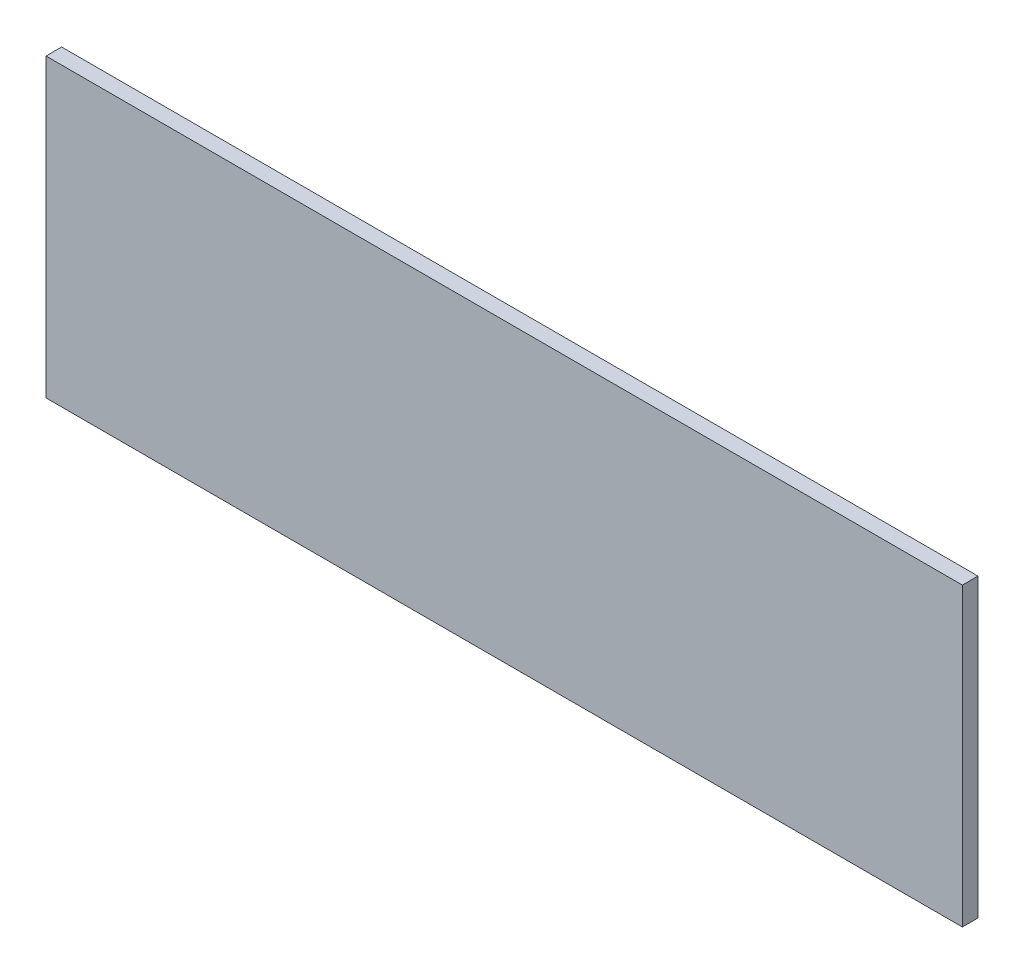
SolidWorks part; units mm, degrees
material "ABS PC"
ref_plane "Front Plane" through (0, 0, 0) normal (0, 0, 1) x (1, 0, 0)
ref_plane "Top Plane" through (0, 0, 0) normal (0, 1, 0) x (1, 0, 0)
ref_plane "Right Plane" through (0, 0, 0) normal (1, 0, 0) x (0, 0, -1)
sketch "Sketch1" plane through (0, 0, 0) normal (0, 0, 1) x (1, 0, 0)
  line L4 (61.722, -172.8154) -> (61.722, -158.3691)
  line L5 (61.722, -158.3691) -> (17.018, -158.3691)
  line L6 (17.018, -158.3691) -> (17.018, -172.8154)
  line L7 (17.018, -172.8154) -> (61.722, -172.8154)
  line L8 (61.722, -172.8154) -> (61.722, -158.3691)
  line L9 (61.722, -158.3691) -> (17.018, -158.3691)
  line L10 (17.018, -158.3691) -> (17.018, -172.8154)
  line L11 (17.018, -172.8154) -> (61.722, -172.8154)
  dimension "D1" = 0
extrude "Boss-Extrude1" add sketch "Sketch1" along normal blind 0.762
